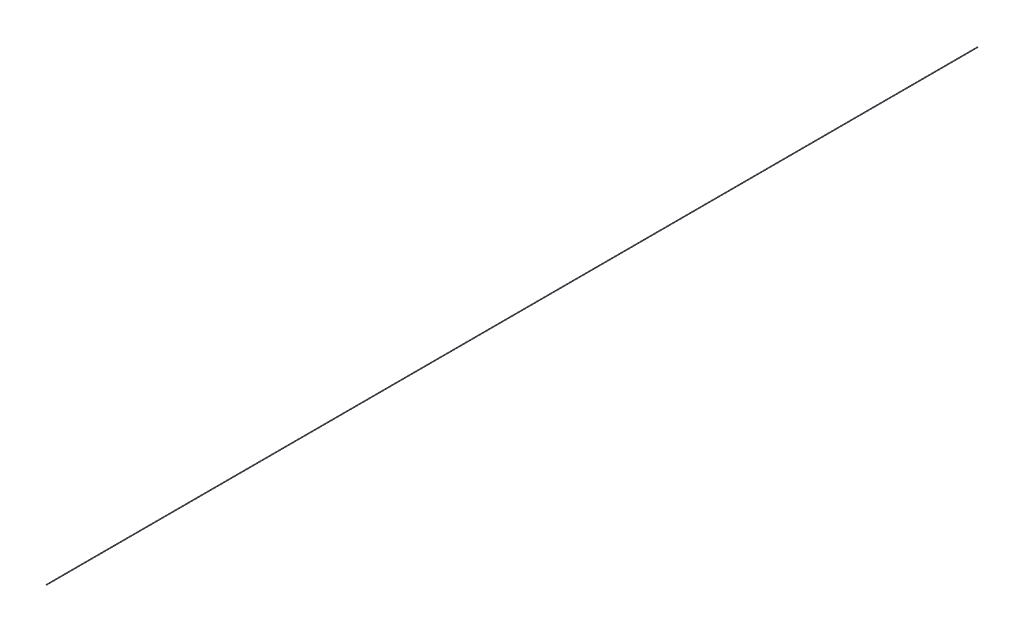
SolidWorks part; units mm, degrees
material "Copper"
ref_plane "Front Plane" through (0, 0, 0) normal (0, 0, 1) x (1, 0, 0)
ref_plane "Top Plane" through (0, 0, 0) normal (0, 1, 0) x (1, 0, 0)
ref_plane "Right Plane" through (0, 0, 0) normal (1, 0, 0) x (0, 0, -1)
sketch "Sketch1" plane through (0, 0, 0) normal (0, 0, 1) x (1, 0, 0)
  circle A0 centre (0, 0) radius 0.25
  dimension "D1" = 0.5
extrude "Boss-Extrude1" add sketch "Sketch1" along normal blind 800
